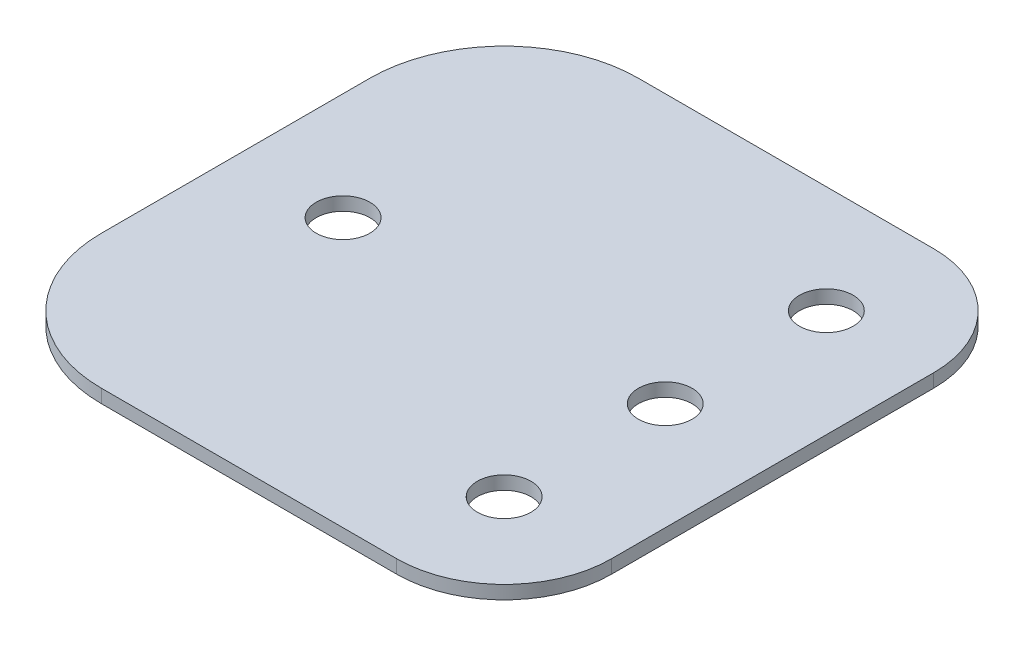
SolidWorks part; units mm, degrees
ref_plane "Front Plane" through (0, 0, 0) normal (0, 0, 1) x (1, 0, 0)
ref_plane "Top Plane" through (0, 0, 0) normal (0, 1, 0) x (1, 0, 0)
ref_plane "Right Plane" through (0, 0, 0) normal (1, 0, 0) x (0, 0, -1)
sketch "Sketch1" plane through (0, 0, 0) normal (0, 1, 0) x (1, 0, 0)
  line L0 (-12.7, 63.5) -> (-12.7, 0) construction
  line L1 (0, 0) -> (-47.625, 0)
  line L2 (0, 0) -> (0, 63.5)
  line L3 (0, 63.5) -> (-47.625, 63.5)
  line L5 (-12.7, 31.75) -> (-25.4, 31.75) construction
  line L6 (-38.1, 44.45) -> (-63.5, 44.45) construction
  line L7 (-38.1, 44.45) -> (-38.1, 19.05) construction
  line L8 (-38.1, 19.05) -> (-63.5, 19.05) construction
  line L9 (-63.5, 44.45) -> (-63.5, 19.05)
  line L10 (-38.1, 44.45) -> (-63.5, 19.05) construction
  line L11 (-38.1, 19.05) -> (-63.5, 44.45) construction
  line L12 (-25.4, 31.75) -> (-38.1, 31.75) construction
  line L13 (-63.5, 44.45) -> (-63.5, 47.625)
  line L14 (-63.5, 19.05) -> (-63.5, 15.875)
  line L15 (-63.5, 47.625) -> (-38.1, 47.625) construction
  line L16 (-38.1, 47.625) -> (-38.1, 44.45) construction
  line L17 (-63.5, 15.875) -> (-38.1, 15.875) construction
  line L18 (-38.1, 15.875) -> (-38.1, 19.05) construction
  circle A0 centre (-12.7, 50.8) radius 3.175
  circle A1 centre (-12.7, 31.75) radius 3.175
  circle A2 centre (-12.7, 12.7) radius 3.175
  circle A3 centre (-50.8, 31.75) radius 3.175
  arc A4 (-63.5, 47.625) -> (-47.625, 63.5) centre (-47.625, 47.625) cw
  arc A5 (-63.5, 15.875) -> (-47.625, 0) centre (-47.625, 15.875) ccw
  arc A7 (0, 50.8) -> (-12.7, 63.5) centre (-12.7, 50.8) ccw
  arc A8 (-12.7, 0) -> (0, 12.7) centre (-12.7, 12.7) ccw
  dimension "D1" = 6.35
  dimension "D2" = 12.7
  dimension "D3" = 12.7
  dimension "D4" = 19.05
  dimension "D5" = 19.05
  dimension "D6" = 12.7
  dimension "D7" = 25.4
  dimension "D8" = 12.7
  dimension "D9" = 12.7
  dimension "D10" = 3.175
extrude "Boss-Extrude1" add sketch "Sketch1" along normal blind 1.5875 contours L1 A8 L2 A7 L3 A4 L13 L9 L14 A5 A0 A1 A2 A3
